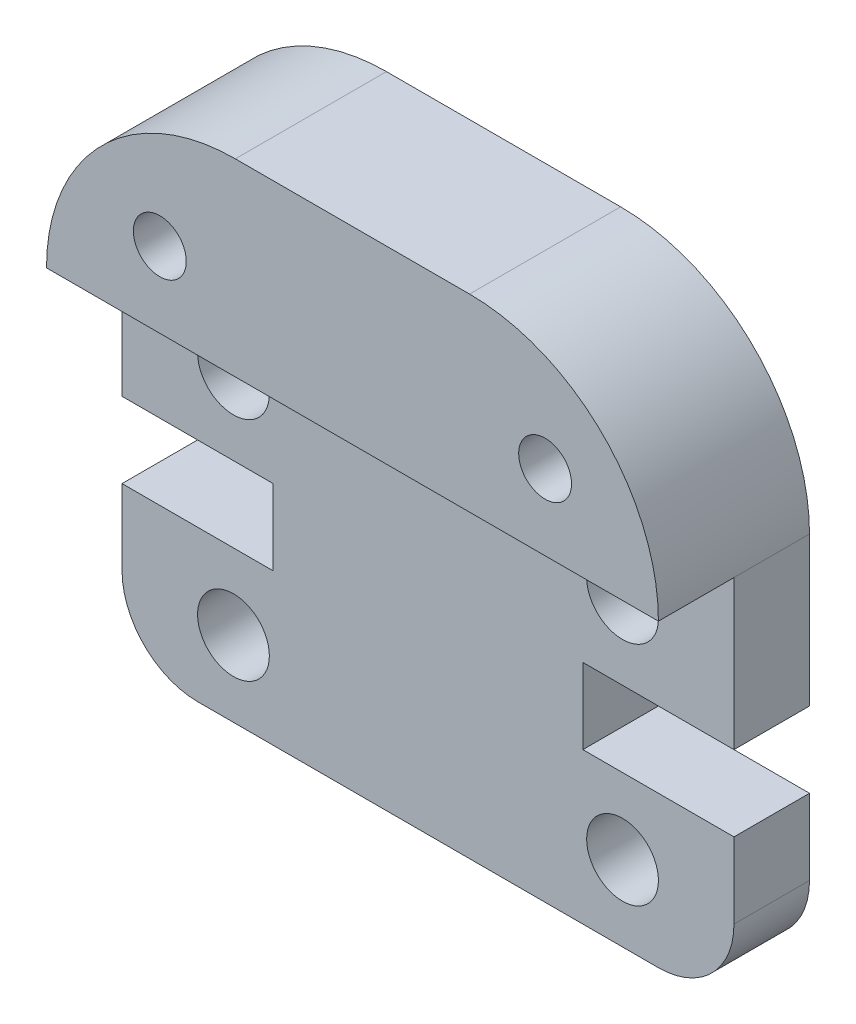
SolidWorks part; units mm, degrees
ref_plane "Front Plane" through (0, 0, 0) normal (0, 0, 1) x (1, 0, 0)
ref_plane "Top Plane" through (0, 0, 0) normal (0, 1, 0) x (1, 0, 0)
ref_plane "Right Plane" through (0, 0, 0) normal (1, 0, 0) x (0, 0, -1)
sketch "Sketch2" plane through (0, 0, 0) normal (0, 0, 1) x (1, 0, 0)
  line L0 (0, 9.945) -> (0, 6)
  line L1 (5, 14.945) -> (11.2, 14.945)
  line L2 (8.1, 14.945) -> (8.1, 0) construction
  line L3 (2, 0) -> (14.2, 0)
  line L4 (12.2, 4) -> (16.2, 4)
  line L5 (12.2, 6) -> (12.2, 4)
  line L6 (16.2, 6) -> (12.2, 6)
  line L7 (16.2, 2) -> (16.2, 4)
  line L8 (16.2, 9.945) -> (16.2, 6)
  line L17 (0, 2) -> (0, 4)
  line L18 (0, 6) -> (4, 6)
  line L20 (4, 6) -> (4, 4)
  line L21 (4, 4) -> (0, 4)
  circle A0 centre (13.25, 8) radius 0.95
  circle A1 centre (13.25, 2) radius 0.95
  arc A2 (16.2, 2) -> (14.2, 0) centre (14.2, 2) cw
  circle A3 centre (13.2, 11.942) radius 0.7
  arc A4 (11.2, 14.945) -> (16.2, 9.945) centre (11.2, 9.945) cw
  arc A11 (5, 14.945) -> (0, 9.945) centre (5, 9.945) ccw
  circle A13 centre (3, 11.942) radius 0.7
  arc A15 (0, 2) -> (2, 0) centre (2, 2) ccw
  circle A17 centre (2.95, 2) radius 0.95
  circle A18 centre (2.95, 8) radius 0.95
  dimension "D1" = 1.4
  dimension "D2" = 1.9
  dimension "D3" = 5
  dimension "D4" = 2
  dimension "D5" = 3
  dimension "D6" = 8.1
  dimension "D7" = 8
  dimension "D8" = 3.003
  dimension "D9" = 14.945
extrude "Boss-Extrude1" add sketch "Sketch2" along normal blind 4
sketch "Sketch3" plane through (0, 0, 4) normal (0, 0, -1) x (-1, 0, 0)
  line L0 (-16.2, 9.945) -> (0, 9.945)
  line L1 (0, 9.945) -> (0, 0)
  line L2 (0, 0) -> (-16.2, 0)
  line L3 (-16.2, 0) -> (-16.2, 9.945)
extrude "Cut-Extrude2" cut sketch "Sketch3" along normal blind 2
equation "\"D6@Sketch2\"= \"fingerWidth@parametersSketch@prostheticParameters.SLDPRT\" / 2'Finger width"
equation "\"D9@Sketch2\"= ( ( \"HL@parametersSketch@prostheticParameters.SLDPRT\" * 0.097 ) - 3 ) 'DIP legth-Silicone Sheet DIP"
equation "\"D1@Sketch2\"= 1 + \"tol1@parametersSketch@prostheticParameters.SLDPRT\""
equation "\"D2@Sketch2\"= 1.5 + \"tol1@parametersSketch@prostheticParameters.SLDPRT\""
